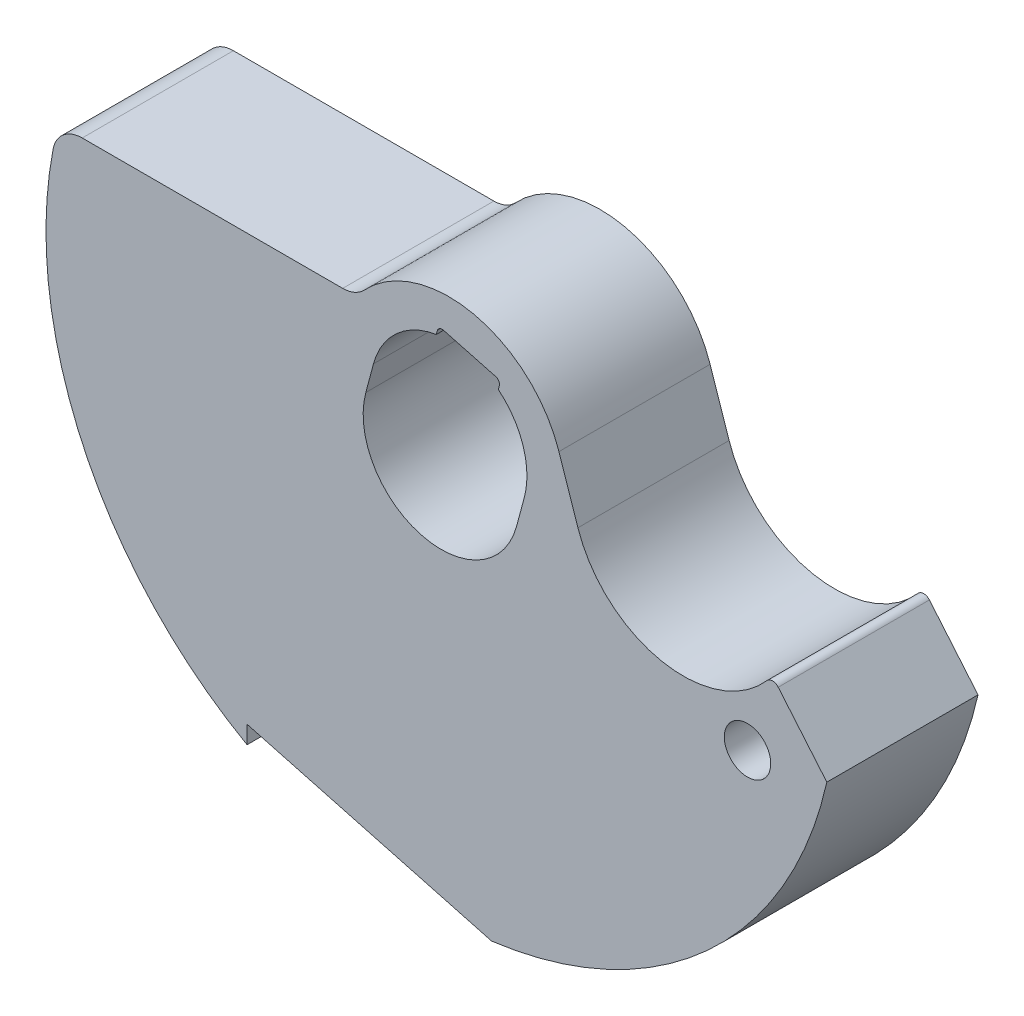
SolidWorks part; units mm, degrees
ref_plane "Front Plane" through (0, 0, 0) normal (0, 0, 1) x (1, 0, 0)
ref_plane "Top Plane" through (0, 0, 0) normal (0, 1, 0) x (1, 0, 0)
ref_plane "Right Plane" through (0, 0, 0) normal (1, 0, 0) x (0, 0, -1)
sketch "Sketch1" plane through (0, 0, 0) normal (0, 0, 1) x (1, 0, 0)
  line L0 (0, 40.7088) -> (0, -42.4788) construction
  line L1 (50.0011, 0) -> (-47.9361, 0) construction
  line L2 (0, 0) -> (4.815, 17.9697) construction
  line L3 (-7.4706, 2.0017) -> (6.4814, -1.7367) construction
  line L4 (-7.0762, 3.4738) -> (6.8758, -0.2646) construction
  line L5 (-3.8765, 1.0387) -> (-3.482, 2.5108)
  line L6 (4.2709, 0.4334) -> (3.8765, -1.0387)
  line L7 (-5.0653, 5.08) -> (-18.4566, 5.08)
  line L8 (6.0531, 3.3717) -> (7.0281, 0.4672)
  line L9 (17.3258, -1.4831) -> (19.8243, -4.4608)
  line L10 (0, 0) -> (7.5113, -8.9516) construction
  line L11 (0, 0) -> (43.883, -11.7584) construction
  line L12 (15.748, 40.7088) -> (15.748, -42.4788) construction
  line L13 (50.0011, -5.08) -> (-47.9361, -5.08) construction
  line L14 (-1.0387, -3.8765) -> (-9.0244, -1.7367) construction
  line L15 (-9.9822, -16.7843) -> (-9.9822, -17.6991)
  line L16 (-9.9822, -16.7843) -> (2.5931, -20.1539)
  line L17 (2.8088, 5.0851) -> (0.11, 5.8082)
  line L18 (1.4594, 5.4467) -> (-6.5263, 7.5864) construction
  line L21 (2.9359, 4.578) -> (2.9884, 4.774)
  line L24 (-0.2536, 5.4326) -> (-0.2011, 5.6286)
  arc A0 (-3.8765, 1.0387) -> (3.8765, -1.0387) centre (0, 0) ccw
  arc A1 (6.1601, -0.0728) -> (6.1791, 0) centre (0.3944, 1.4721) ccw
  arc A2 (4.2709, 0.4334) -> (2.9359, 4.578) centre (0.3944, 1.4721) ccw
  arc A3 (7.0281, 0.4672) -> (16.7472, -1.4771) centre (12.446, 2.286) ccw
  arc A4 (6.0531, 3.3717) -> (-3.9548, 5.5602) centre (0.3944, 1.4721) ccw
  arc A5 (-19.953, 3.8443) -> (-9.9822, -17.6991) centre (0, 0) ccw
  arc A6 (16.7472, -1.4771) -> (17.3258, -1.4831) centre (17.0339, -1.728) cw
  arc A7 (2.5931, -20.1539) -> (19.8243, -4.4608) centre (0, 0) ccw
  arc A8 (-18.4566, 5.08) -> (-19.953, 3.8443) centre (-18.4566, 3.556) ccw
  arc A9 (-5.0653, 5.08) -> (-3.9548, 5.5602) centre (-5.0653, 6.604) ccw
  circle A10 centre (15.748, -5.08) radius 1.1938
  arc A11 (-0.2536, 5.4326) -> (-3.482, 2.5108) centre (0.3944, 1.4721) ccw
  arc A12 (2.8088, 5.0851) -> (2.9884, 4.774) centre (2.7431, 4.8397) cw
  arc A13 (-0.2011, 5.6286) -> (0.11, 5.8082) centre (0.0443, 5.5629) cw
  point P35 (-9.9822, 40.7088)
  point P36 (-9.9822, -42.4788)
  point P48 (1.5947, -0.4273)
  point P50 (6.4097, 17.5424)
  point P51 (-1.5947, 0.4273)
  point P52 (3.2202, 18.397)
  dimension "D1" = 8.0264
  dimension "D4" = 11.938
  dimension "D6" = 11.43
  dimension "D11" = 40.64
  dimension "D12" = 0.381
  dimension "D16" = 1.524
  dimension "D17" = 1.524
  dimension "D20" = 2.3876
  dimension "D24" = 0.254
  dimension "D2" = 15
  dimension "D5" = 5.08
  dimension "D7" = 2.286
  dimension "D8" = 12.446
  dimension "D9" = 50
  dimension "D10" = 12.319
  dimension "D13" = 15
  dimension "D14" = 18.796
  dimension "D15" = 9.9822
  dimension "D22" = 3.302
  dimension "D23" = 1.651
  dimension "D3" = 1.524
  dimension "D18" = 15.748
  dimension "D19" = 5.08
  dimension "D21" = 9.652
extrude "Boss-Extrude1" add sketch "Sketch1" against normal blind 7.7724
